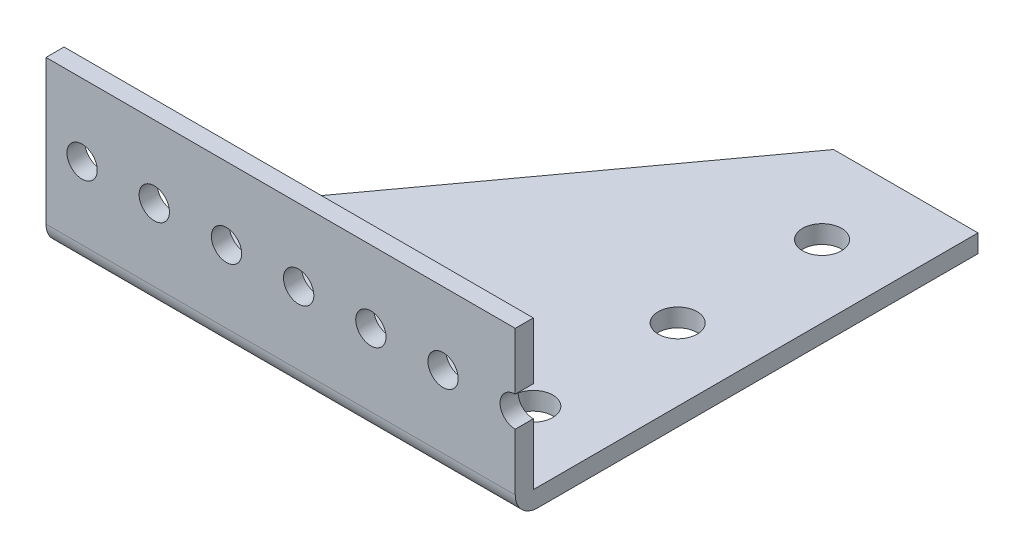
SolidWorks part; units mm, degrees
ref_plane "Front Plane" through (0, 0, 0) normal (0, 0, 1) x (1, 0, 0)
ref_plane "Top Plane" through (0, 0, 0) normal (0, 1, 0) x (1, 0, 0)
ref_plane "Right Plane" through (0, 0, 0) normal (1, 0, 0) x (0, 0, -1)
sketch "Sketch1" plane through (0, 0, 0) normal (0, 1, 0) x (1, 0, 0)
  line L0 (41.275, -40.7035) -> (41.275, 40.7035)
  line L1 (41.275, 40.7035) -> (-41.275, 40.7035)
  line L3 (-41.275, -40.7035) -> (-41.275, 40.7035)
  line L4 (-41.275, -40.7035) -> (41.275, -40.7035)
  line L5 (41.275, 40.7035) -> (-41.275, -40.7035) construction
  line L6 (0, -55) -> (0, 55) construction
  line L7 (-55, 0) -> (55, 0) construction
  point P2 (0, 0)
  dimension "D2" = 81.407
  dimension "D1" = 82.55
extrude "Boss-Extrude1" add sketch "Sketch1" along normal blind 3.175 from offset 34.925 offset against normal yes
sketch "Sketch3" plane through (0, -31.75, 0) normal (0, 1, 0) x (1, 0, 0)
  line L0 (41.275, -40.7035) -> (-41.275, -40.7035)
  line L1 (-41.275, -40.7035) -> (-41.275, -37.5285)
  line L2 (-41.275, -37.5285) -> (41.275, -37.5285)
  line L3 (-41.275, -40.7035) -> (41.275, -40.7035) construction
  line L4 (41.275, -40.7035) -> (41.275, -37.5285)
  line L5 (-41.275, 40.7035) -> (-41.275, -40.7035) construction
  line L6 (41.275, -40.7035) -> (41.275, 40.7035) construction
  dimension "D1" = 3.175
extrude "Boss-Extrude2" add sketch "Sketch3" along normal blind 50.8
hole_wizard "#10 Clearance Hole2" positions "Sketch7" profile "Sketch6" hole size "#10" standard "ANSI Inch" end condition through all
sketch "Sketch7" plane through (0, 0, -40.7035) normal (0, 0, -1) x (-1, 0, 0)
  line L2 (-41.275, -18.288) -> (34.925, -18.288) construction
  line L5 (-41.275, 7.112) -> (34.925, 7.112) construction
  line L8 (41.275, 19.05) -> (41.275, -31.75) construction
  line L9 (-41.275, 19.05) -> (-41.275, -31.75) construction
  line L10 (-41.275, 19.05) -> (41.275, 19.05) construction
  point P56 (22.225, 7.112)
  point P57 (9.525, 7.112)
  point P58 (-3.175, 7.112)
  point P59 (-15.875, 7.112)
  point P61 (-28.575, 7.112)
  point P118 (22.225, -18.288)
  point P119 (9.525, -18.288)
  point P120 (-3.175, -18.288)
  point P121 (-15.875, -18.288)
  point P123 (-28.575, -18.288)
  point P157 (34.925, 7.112)
  point P159 (34.925, -18.288)
  point P185 (-41.275, 7.112)
  point P189 (-41.275, -18.288)
  dimension "D1" = 6.35
  dimension "D2" = 11.938
  dimension "D3" = 12.7
  dimension "D4" = 25.4
  dimension "D5" = 12.7
  dimension "D6" = 12.7
  dimension "D7" = 12.7
  dimension "D8" = 12.7
  dimension "D10" = 12.7
sketch "Sketch6" plane through (-22.225, 7.112, -40.7035) normal (1, 0, 0) x (0, 1, 0)
  line L0 (0, 0) -> (0, 81.407)
  line L1 (0, 81.407) -> (2.667, 81.407)
  line L2 (2.667, 81.407) -> (2.667, 0)
  line L5 (2.667, 0) -> (0, 0)
  line L11 (0, -6.35) -> (0, 107.95) construction
  dimension "Thru Hole Dia." = 5.334
  dimension "Thru Hole Depth" = 81.407
chamfer "Chamfer1" distance 3.175 angle 45 1 edges at (-41.275, 19.05, 39.116)
fillet "Fillet2" radius 3.937 1 edges at (0, -34.925, 40.7035)
sketch "Sketch9" plane through (0, -34.925, 0) normal (0, -1, 0) x (1, 0, 0)
  line L0 (-41.275, 37.5285) -> (15.875, -40.7035)
  line L1 (-41.275, -40.7035) -> (-41.275, 36.7665) construction
  line L2 (41.275, -40.7035) -> (-41.275, -40.7035) construction
  line L3 (41.275, 36.7665) -> (41.275, -40.7035) construction
  line L4 (15.875, -40.7035) -> (-41.275, -40.7035)
  line L5 (-41.275, -40.7035) -> (-41.275, 37.5285)
  line L6 (-41.275, 40.7035) -> (41.275, 40.7035) construction
  line L7 (28.575, -40.7035) -> (28.575, 36.7665) construction
  line L8 (41.275, 36.7665) -> (-41.275, 36.7665) construction
  line L9 (41.275, 37.5285) -> (-41.275, 37.5285) construction
  circle A0 centre (34.925, 23.9395) radius 3.429 construction
  circle A1 centre (34.925, 11.2395) radius 3.429 construction
  circle A2 centre (34.925, -1.4605) radius 3.429 construction
  circle A3 centre (28.575, 24.8285) radius 3.429
  circle A7 centre (28.575, -0.5715) radius 3.429
  circle A8 centre (28.575, -25.9715) radius 3.429
  dimension "D3" = 6.858
  dimension "D7" = 16.764
  dimension "D9" = 6.858
  dimension "D10" = 12.7
  dimension "D11" = 3
  dimension "D12" = 25.4
  dimension "D1" = 25.4
  dimension "D2" = 0
  dimension "D4" = 12.7
  dimension "D5" = 12.7
  dimension "D6" = 6.35
  dimension "D8" = 12.7
extrude "Cut-Extrude2" cut sketch "Sketch9" against normal through all
sketch "Sketch10" plane through (0, 0, 40.7035) normal (0, 0, 1) x (1, 0, 0)
  line L0 (41.275, -5.588) -> (-41.275, -5.588)
  line L1 (41.275, 4.445) -> (41.275, -15.621) construction
  line L2 (-41.275, 15.875) -> (-41.275, -30.988) construction
  line L3 (-41.275, -5.588) -> (-41.275, 19.05)
  line L4 (-41.275, 19.05) -> (41.275, 19.05)
  line L5 (41.275, 19.05) -> (41.275, -5.588)
extrude "Cut-Extrude3" cut sketch "Sketch10" against normal through all
